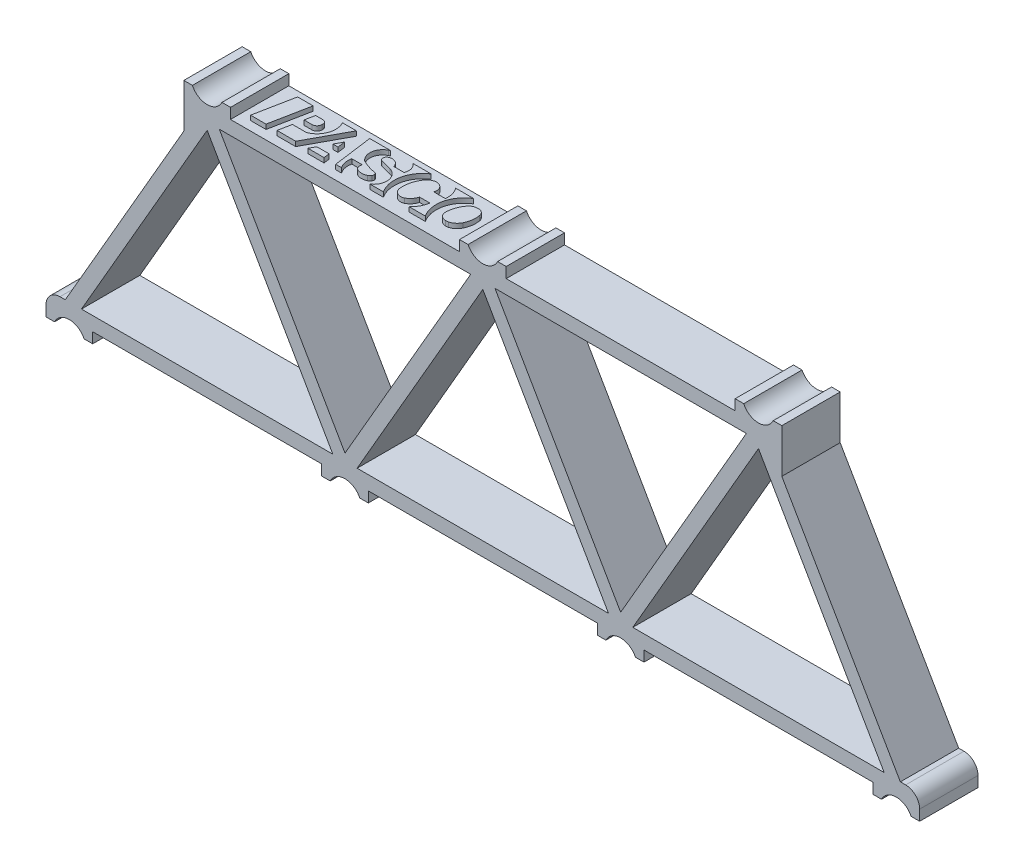
SolidWorks part; units mm, degrees
ref_plane "Front XY" through (0, 0, 0) normal (0, 0, 1) x (1, 0, 0)
ref_plane "Top XZ" through (0, 0, 0) normal (0, 1, 0) x (1, 0, 0)
ref_plane "Right YZ" through (0, 0, 0) normal (1, 0, 0) x (0, 0, -1)
sketch "Sketch1" plane through (0, 0, 0) normal (0, 0, 1) x (1, 0, 0)
  line L0 (-45, -25.9808) -> (-15, -25.9808) construction
  line L1 (-15, -25.9808) -> (15, -25.9808) construction
  line L2 (15, -25.9808) -> (45, -25.9808) construction
  line L3 (-45, -25.9808) -> (-30, 0) construction
  line L4 (-30, 0) -> (-15, -25.9808) construction
  line L5 (-15, -25.9808) -> (0, 0) construction
  line L6 (0, 0) -> (15, -25.9808) construction
  line L7 (15, -25.9808) -> (30, 0) construction
  line L8 (30, 0) -> (45, -25.9808) construction
  line L9 (-30, 0) -> (0, 0) construction
  line L10 (0, 0) -> (30, 0) construction
  line L11 (-43.6802, -25.2188) -> (-30, -1.524)
  line L12 (-30, -1.524) -> (-16.3198, -25.2188)
  line L13 (-43.6802, -25.2188) -> (-16.3198, -25.2188)
  line L14 (-28.6802, -0.762) -> (-15, -24.4568)
  line L15 (-15, -24.4568) -> (-1.3198, -0.762)
  line L16 (-28.6802, -0.762) -> (-1.3198, -0.762)
  line L17 (-13.6802, -25.2188) -> (0, -1.524)
  line L18 (0, -1.524) -> (13.6802, -25.2188)
  line L19 (-13.6802, -25.2188) -> (13.6802, -25.2188)
  line L20 (1.3198, -0.762) -> (15, -24.4568)
  line L21 (15, -24.4568) -> (28.6802, -0.762)
  line L22 (1.3198, -0.762) -> (28.6802, -0.762)
  line L23 (16.3198, -25.2188) -> (30, -1.524)
  line L24 (30, -1.524) -> (43.6802, -25.2188)
  line L25 (16.3198, -25.2188) -> (43.6802, -25.2188)
  line L26 (-46.3198, -26.7428) -> (-30.4399, 0.762)
  line L27 (-30.4399, 0.762) -> (0, 0.762)
  line L28 (0, 0.762) -> (30.4399, 0.762)
  line L29 (30.4399, 0.762) -> (46.3198, -26.7428)
  line L30 (15, -26.7428) -> (46.3198, -26.7428)
  line L31 (-15, -26.7428) -> (15, -26.7428)
  line L32 (-46.3198, -26.7428) -> (-15, -26.7428)
  dimension "D1" = 60
  dimension "D2" = 30
extrude "Boss-Extrude1" add sketch "Sketch1" along normal mid plane 6.35
sketch "Sketch2" plane through (0, 0, 0) normal (0, 0, 1) x (1, 0, 0)
  line L0 (-45, -25.9808) -> (-45, -28.6478) construction
  line L1 (-46.3198, -26.7428) -> (-15, -26.7428) construction
  line L2 (-46.6064, -27.8858) -> (-47.54, -27.8858)
  line L3 (-47.54, -27.8858) -> (-47.54, -25.2188)
  line L4 (-43.3936, -27.8858) -> (-42.46, -27.8858)
  line L5 (-42.46, -27.8858) -> (-42.46, -25.2188)
  line L6 (-42.46, -25.2188) -> (-47.54, -25.2188)
  line L7 (-27.46, 0.762) -> (-30.4399, 0.762)
  line L8 (-15, -25.9808) -> (-15, -28.6478) construction
  line L9 (-16.6064, -27.8858) -> (-17.54, -27.8858)
  line L10 (-17.54, -27.8858) -> (-17.54, -26.7428)
  line L11 (-13.3936, -27.8858) -> (-12.46, -27.8858)
  line L12 (-12.46, -27.8858) -> (-12.46, -26.7428)
  line L13 (-12.46, -26.7428) -> (-17.54, -26.7428)
  line L14 (-30.4399, 0.762) -> (0, 0.762) construction
  line L15 (-30, 0) -> (-30, 2.667) construction
  line L16 (-27.46, 0.762) -> (-27.46, 1.905)
  line L17 (-27.46, 1.905) -> (-28.3936, 1.905)
  line L18 (-32.54, 0.762) -> (-32.54, 1.905)
  line L19 (-32.54, 1.905) -> (-31.6064, 1.905)
  line L20 (-30.4399, 0.762) -> (-32.54, -2.8754)
  line L21 (-46.3198, -26.7428) -> (-30.4399, 0.762) construction
  line L22 (-32.54, -2.8754) -> (-32.54, 0.762)
  line L23 (-46.3198, -26.7428) -> (46.3198, -26.7428) construction
  line L24 (-43.6802, -25.2188) -> (-16.3198, -25.2188) construction
  arc A0 (-43.3936, -27.8858) -> (-46.6064, -27.8858) centre (-45, -28.6478) ccw
  arc A1 (-13.3936, -27.8858) -> (-16.6064, -27.8858) centre (-15, -28.6478) ccw
  arc A2 (-31.6064, 1.905) -> (-28.3936, 1.905) centre (-30, 2.667) ccw
  dimension "D1" = 1.778
  dimension "D4" = 1.778
  dimension "D9" = 5.08
  dimension "D2" = 1.905
  dimension "D3" = 1.143
  dimension "D5" = 5.08
  dimension "D6" = 1.143
  dimension "D7" = 5.08
  dimension "D8" = 1.143
extrude "Boss-Extrude2" add sketch "Sketch2" against normal up to surface (3.175 mm away) and the other way up to surface (3.175 mm away) up to face at (15, -8.6603, -3.175) other way up to face at (15, -8.6603, 3.175)
sketch "Sketch3" plane through (0, 0, 0) normal (0, 0, 1) x (1, 0, 0)
  line L0 (0, 0) -> (0, 2.667) construction
  line L1 (1.6064, 1.905) -> (2.54, 1.905)
  line L2 (2.54, 1.905) -> (2.54, 0.762)
  line L3 (0, 0.762) -> (30.4399, 0.762) construction
  line L4 (2.54, 0.762) -> (-2.54, 0.762)
  line L5 (-30.4399, 0.762) -> (0, 0.762) construction
  line L6 (-2.54, 1.905) -> (-2.54, 0.762)
  line L7 (-1.6064, 1.905) -> (-2.54, 1.905)
  line L9 (-12.46, -26.7428) -> (-17.54, -26.7428) construction
  line L10 (-45, -25.9808) -> (-45, -28.6478) construction
  arc A0 (-1.6064, 1.905) -> (1.6064, 1.905) centre (0, 2.667) ccw
  arc A1 (-43.3936, -27.8858) -> (-46.6064, -27.8858) centre (-45, -28.6478) ccw construction
  dimension "D1" = 1.143
extrude "Boss-Extrude3" add sketch "Sketch3" against normal up to surface and the other way up to surface
fillet "Fillet1" radius 1.524 1 edges at (-47.54, -25.2188, 0)
mirror "Mirror1" about plane through (0, 0, 0) normal (1, 0, 0) of "Fillet1", "Boss-Extrude2"
sketch "Sketch4" plane through (30.3415, 0.762, -10.9983) normal (0, 1, 0) x (-1, 0, 0)
  line L0 (55.7666, 8.903) -> (54.0822, 8.903)
  line L1 (54.0822, 8.903) -> (54.9244, 13.1845)
  line L2 (56.6089, 13.1845) -> (55.7666, 8.903)
  line L3 (54.9244, 13.1845) -> (56.6089, 13.1845)
  line L4 (49.3737, 8.903) -> (51.6958, 13.1845)
  line L5 (53.7312, 13.1845) -> (53.4551, 11.7807)
  line L6 (47.3442, 13.1845) -> (47.9247, 8.903)
  line L7 (52.3626, 10.7279) -> (53.248, 10.7279)
  line L8 (53.248, 10.7279) -> (53.0409, 9.6751)
  line L9 (53.0409, 9.6751) -> (52.2241, 9.6751)
  line L10 (51.8362, 10.0631) -> (51.8362, 10.2015)
  line L11 (50.8536, 8.9732) -> (50.8886, 8.903)
  line L12 (50.8886, 8.903) -> (49.3737, 8.903)
  line L13 (53.4551, 11.7807) -> (52.0448, 11.7807)
  line L14 (48.9585, 10.5963) -> (48.8455, 11.4298)
  line L15 (48.8455, 11.4298) -> (49.4106, 11.4298)
  line L16 (49.4106, 11.4298) -> (48.9585, 10.5963)
  line L17 (45.6575, 8.903) -> (45.8001, 8.9732)
  line L18 (45.8829, 12.0583) -> (45.8829, 11.7807)
  line L19 (45.8829, 11.7807) -> (46.9933, 11.7807)
  line L20 (47.9247, 8.903) -> (45.6575, 8.903)
  line L21 (51.6958, 13.1845) -> (53.7312, 13.1845)
  line L22 (48.6076, 13.1845) -> (50.3622, 13.1845)
  line L23 (46.7125, 13.1845) -> (47.3442, 13.1845)
  line L24 (50.0196, 12.5528) -> (48.6932, 12.5528)
  line L25 (50.3622, 13.1845) -> (50.0196, 12.5528)
  line L26 (48.6932, 12.5528) -> (48.6076, 13.1845)
  line L27 (43.0934, 9.0079) -> (43.2038, 8.8974)
  line L28 (43.2038, 8.8974) -> (41.2386, 8.8974)
  line L29 (44.0085, 10.6319) -> (45.1372, 10.3497)
  line L30 (43.9769, 10.232) -> (42.8539, 10.232)
  line L31 (38.5708, 8.903) -> (36.6056, 8.903)
  line L32 (38.5708, 11.7105) -> (39.6938, 11.7105)
  line L33 (39.4131, 10.4472) -> (38.1497, 10.4472)
  line L34 (42.1504, 13.1845) -> (43.6243, 13.1845)
  line L35 (37.5882, 13.1845) -> (39.3429, 13.1845)
  line L36 (35.481, 9.6026) -> (35.3569, 9.6026)
  arc A0 (46.0025, 11.3297) -> (44.4424, 11.8336) centre (43.5988, 6.5555) ccw
  arc A1 (45.5669, 12.5268) -> (44.5843, 12.5069) centre (45.0989, 11.369) ccw
  arc A2 (45.3751, 9.9924) -> (45.1372, 10.3497) centre (45.0598, 10.0403) ccw
  arc A3 (45.0793, 9.6312) -> (45.3751, 9.9924) centre (44.9228, 10.0611) ccw
  arc A4 (45.8829, 12.0583) -> (45.5669, 12.5268) centre (45.3775, 12.0583) ccw
  arc A5 (46.9933, 11.7807) -> (46.7125, 13.1845) centre (45.2737, 12.1667) ccw
  arc A6 (51.8362, 10.0631) -> (52.2241, 9.6751) centre (52.2241, 10.0631) ccw
  arc A7 (52.3626, 10.7279) -> (51.8362, 10.2015) centre (52.3626, 10.2015) ccw
  arc A8 (52.0448, 11.7807) -> (51.7548, 11.7109) centre (52.0448, 11.1429) ccw
  arc A9 (51.7548, 11.7109) -> (50.8536, 8.9732) centre (52.6862, 9.8871) ccw
  arc A10 (45.8001, 8.9732) -> (46.1639, 11.2138) centre (45.1852, 10.2229) ccw
  arc A11 (46.1639, 11.2138) -> (46.0025, 11.3297) centre (45.7157, 10.76) ccw
  arc A12 (35.481, 9.6026) -> (36.2948, 10.0199) centre (35.481, 10.6046) ccw
  arc A13 (36.8641, 11.666) -> (36.0777, 12.512) centre (36.0532, 11.7008) ccw
  arc A14 (44.3262, 12.272) -> (44.2646, 12.0208) centre (44.6418, 12.0615) ccw
  arc A15 (41.2386, 8.8974) -> (42.1504, 13.1845) centre (39.5781, 11.491) ccw
  arc A16 (43.6243, 13.1845) -> (43.6095, 10.8085) centre (44.3995, 11.9916) ccw
  arc A17 (36.6056, 8.903) -> (37.5882, 13.1845) centre (35.0592, 11.5114) ccw
  arc A18 (39.3429, 13.1845) -> (38.5708, 11.7105) centre (41.058, 11.3469) ccw
  arc A19 (40.4153, 12.6039) -> (39.6938, 11.7105) centre (41.058, 11.3469) ccw
  arc A20 (41.5918, 11.9736) -> (40.4153, 12.6039) centre (40.7812, 11.8738) ccw
  arc A21 (44.2646, 12.0208) -> (44.4424, 11.8336) centre (44.476, 12.0436) ccw
  arc A22 (43.6095, 10.8085) -> (44.0085, 10.6319) centre (44.3179, 11.8694) ccw
  arc A23 (43.9769, 10.232) -> (45.0793, 9.6312) centre (44.793, 10.4176) ccw
  arc A24 (42.8539, 10.232) -> (43.0934, 9.0079) centre (43.8833, 9.7978) ccw
  arc A25 (41.1552, 9.9997) -> (41.5918, 11.9736) centre (38.5855, 11.6033) ccw
  arc A26 (40.2511, 9.3719) -> (41.1552, 9.9997) centre (40.1216, 10.5232) ccw
  arc A27 (39.4131, 10.4472) -> (40.2511, 9.3719) centre (40.1617, 10.1664) ccw
  arc A28 (38.1497, 10.4472) -> (38.5708, 8.903) centre (40.1617, 10.1664) ccw
  arc A29 (36.2948, 10.0199) -> (36.8641, 11.666) centre (33.8223, 11.7965) ccw
  arc A30 (44.5843, 12.5069) -> (44.3262, 12.272) centre (44.8175, 11.9913) ccw
  arc A31 (35.7478, 12.4758) -> (34.9205, 11.7781) centre (36.1351, 11.1771) ccw
  arc A32 (34.6919, 10.1578) -> (35.3569, 9.6026) centre (35.3569, 10.2783) ccw
  arc A33 (34.9205, 11.7781) -> (34.6919, 10.1578) centre (37.2562, 10.6225) ccw
  arc A34 (36.0777, 12.512) -> (35.7478, 12.4758) centre (36.0417, 11.3183) ccw
extrude "Boss-Extrude4" add sketch "Sketch4" along normal blind 0.508
